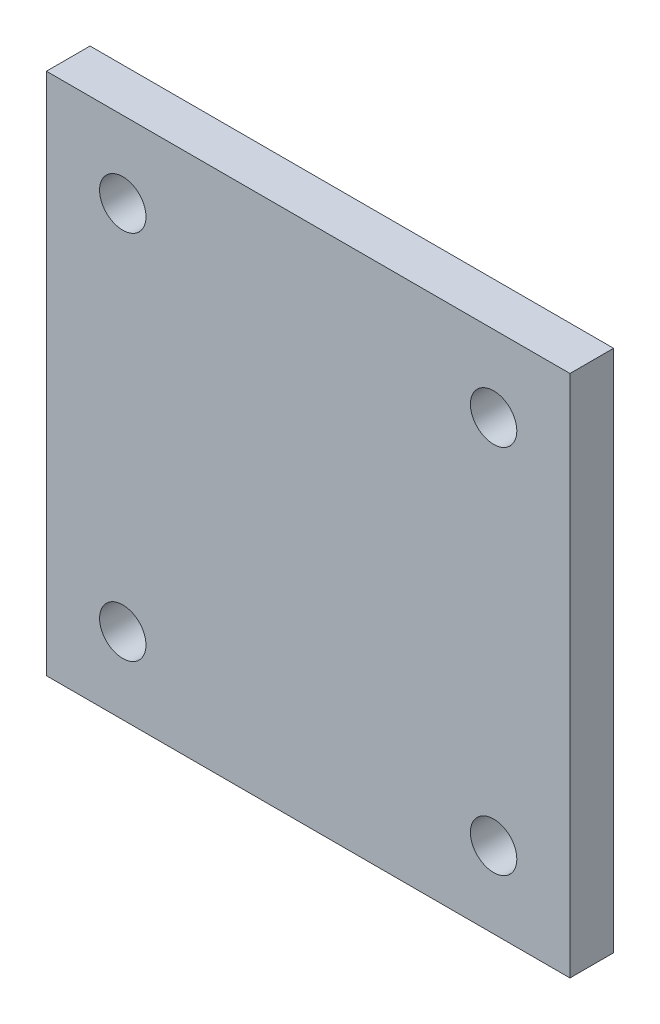
SolidWorks part; units mm, degrees
material "Plain Carbon Steel"
ref_plane "Front Plane" through (0, 0, 0) normal (0, 0, 1) x (1, 0, 0)
ref_plane "Top Plane" through (0, 0, 0) normal (0, 1, 0) x (1, 0, 0)
ref_plane "Right Plane" through (0, 0, 0) normal (1, 0, 0) x (0, 0, -1)
sketch "Sketch1" plane through (0, 0, 0) normal (0, 0, 1) x (1, 0, 0)
  line L1 (-38.1, -38.1) -> (38.1, -38.1)
  line L2 (-38.1, -38.1) -> (-38.1, 38.1)
  line L3 (-38.1, 38.1) -> (38.1, 38.1)
  line L4 (38.1, -38.1) -> (38.1, 38.1)
  line L5 (-38.1, -38.1) -> (38.1, 38.1) construction
  line L6 (-38.1, 38.1) -> (38.1, -38.1) construction
  point P0 (0, 0)
  dimension "D1" = 76.2
extrude "Extrude1" add sketch "Sketch1" along normal blind 6.35
sketch "Sketch2" plane through (0, 0, 6.35) normal (0, 0, 1) x (1, 0, 0)
  line L1 (-26.9875, -26.9875) -> (26.9875, -26.9875) construction
  line L2 (-26.9875, -26.9875) -> (-26.9875, 26.9875) construction
  line L3 (-26.9875, 26.9875) -> (26.9875, 26.9875) construction
  line L4 (26.9875, -26.9875) -> (26.9875, 26.9875) construction
  line L5 (-26.9875, -26.9875) -> (26.9875, 26.9875) construction
  line L6 (-26.9875, 26.9875) -> (26.9875, -26.9875) construction
  point P0 (0, 0)
  dimension "D1" = 53.975
hole_wizard "1/4 Clearance Hole1" positions "Sketch4" profile "Sketch5" hole size "1/4" standard "Ansi Inch" end condition through all
sketch "Sketch4" plane through (0, 0, 6.35) normal (0, 0, 1) x (1, 0, 0)
  point P1 (-26.9875, 26.9875)
  point P4 (26.9875, 26.9875)
  point P7 (26.9875, -26.9875)
  point P10 (-26.9875, -26.9875)
sketch "Sketch5" plane through (-26.9875, 26.9875, 6.35) normal (1, 0, 0) x (0, -1, 0)
  line L0 (0, 0) -> (0, 6.35)
  line L1 (0, 6.35) -> (3.3782, 6.35)
  line L2 (3.3782, 6.35) -> (3.3782, 0)
  line L5 (3.3782, 0) -> (0, 0)
  line L11 (0, -6.35) -> (0, 107.95) construction
  dimension "Thru Hole Dia." = 6.7564
  dimension "Thru Hole Depth" = 6.35
